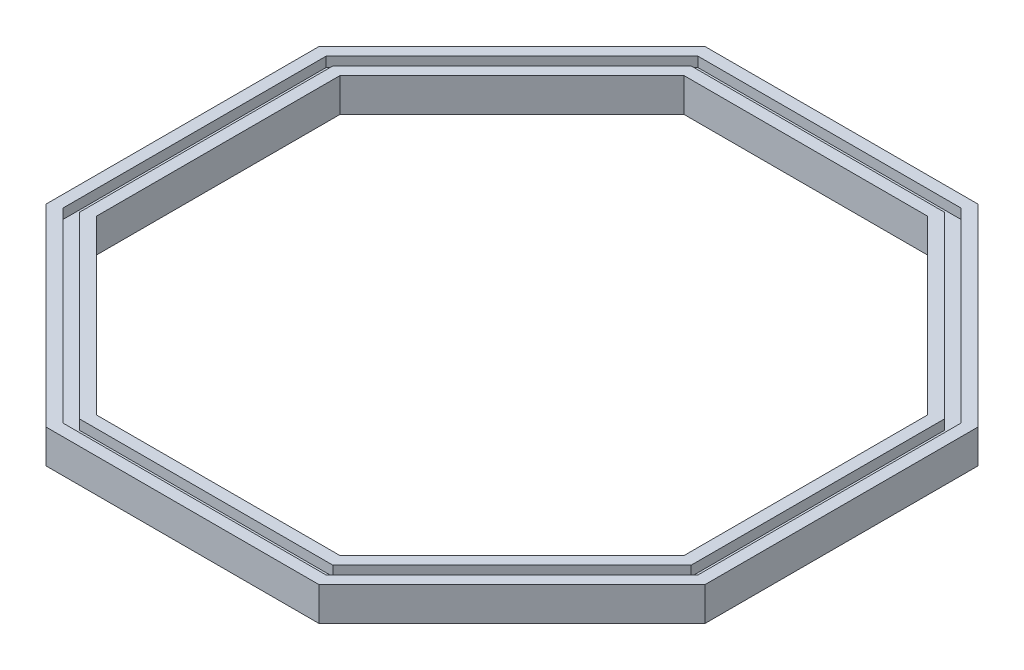
SolidWorks part; units mm, degrees
ref_plane "정면" through (0, 0, 0) normal (0, 0, 1) x (1, 0, 0)
ref_plane "윗면" through (0, 0, 0) normal (0, 1, 0) x (1, 0, 0)
ref_plane "우측면" through (0, 0, 0) normal (1, 0, 0) x (0, 0, -1)
sketch "스케치1" plane through (0, 0, 0) normal (0, 1, 0) x (1, 0, 0)
  line L0 (-55, 0) -> (55, 0) construction
  line L1 (13.2795, -32.0597) -> (32.0597, -13.2795)
  line L2 (32.0597, -13.2795) -> (32.0597, 13.2795)
  line L3 (32.0597, 13.2795) -> (13.2795, 32.0597)
  line L4 (13.2795, 32.0597) -> (-13.2795, 32.0597)
  line L5 (-13.2795, 32.0597) -> (-32.0597, 13.2795)
  line L6 (-32.0597, 13.2795) -> (-32.0597, -13.2795)
  line L7 (-32.0597, -13.2795) -> (-13.2795, -32.0597)
  line L8 (-13.2795, -32.0597) -> (13.2795, -32.0597)
  line L9 (13.7766, -33.2597) -> (33.2597, -13.7766)
  line L10 (33.2597, -13.7766) -> (33.2597, 13.7766)
  line L11 (33.2597, 13.7766) -> (13.7766, 33.2597)
  line L12 (13.7766, 33.2597) -> (-13.7766, 33.2597)
  line L13 (-13.7766, 33.2597) -> (-33.2597, 13.7766)
  line L14 (-33.2597, 13.7766) -> (-33.2597, -13.7766)
  line L15 (-33.2597, -13.7766) -> (-13.7766, -33.2597)
  line L16 (-13.7766, -33.2597) -> (13.7766, -33.2597)
  line L17 (12.7825, -30.8597) -> (30.8597, -12.7825)
  line L18 (30.8597, -12.7825) -> (30.8597, 12.7825)
  line L19 (30.8597, 12.7825) -> (12.7825, 30.8597)
  line L20 (12.7825, 30.8597) -> (-12.7825, 30.8597)
  line L21 (-12.7825, 30.8597) -> (-30.8597, 12.7825)
  line L22 (-30.8597, 12.7825) -> (-30.8597, -12.7825)
  line L23 (-30.8597, -12.7825) -> (-12.7825, -30.8597)
  line L24 (-12.7825, -30.8597) -> (12.7825, -30.8597)
  circle A0 centre (0, 0) radius 34.7011 construction
  dimension "D1" = 72
  dimension "D2" = 1.2
  dimension "D3" = 1.2
extrude "보스-돌출1" add sketch "스케치1" along normal blind 1.7 contours L15 L16 L9 L10 L11 L12 L13 L14 L8 L7 L6 L5 L4 L3 L2 L1 | L7 L8 L1 L2 L3 L4 L5 L6 L24 L23 L22 L21 L20 L19 L18 L17 | L23 L24 L17 L18 L19 L20 L21 L22
sketch "스케치2" plane through (0, 1.7, 0) normal (0, 1, 0) x (1, 0, 0)
  line L8 (-30.8597, -12.7825) -> (-12.7825, -30.8597)
  line L9 (-12.7825, -30.8597) -> (12.7825, -30.8597)
  line L10 (12.7825, -30.8597) -> (30.8597, -12.7825)
  line L11 (30.8597, -12.7825) -> (30.8597, 12.7825)
  line L12 (30.8597, 12.7825) -> (12.7825, 30.8597)
  line L13 (12.7825, 30.8597) -> (-12.7825, 30.8597)
  line L14 (-12.7825, 30.8597) -> (-30.8597, 12.7825)
  line L15 (-30.8597, 12.7825) -> (-30.8597, -12.7825)
  line L16 (-32.0597, -13.2795) -> (-13.2795, -32.0597)
  line L17 (-13.2795, -32.0597) -> (13.2795, -32.0597)
  line L18 (13.2795, -32.0597) -> (32.0597, -13.2795)
  line L19 (32.0597, -13.2795) -> (32.0597, 13.2795)
  line L20 (32.0597, 13.2795) -> (13.2795, 32.0597)
  line L21 (13.2795, 32.0597) -> (-13.2795, 32.0597)
  line L22 (-13.2795, 32.0597) -> (-32.0597, 13.2795)
  line L23 (-32.0597, 13.2795) -> (-32.0597, -13.2795)
  line L24 (-32.0597, -13.2795) -> (-13.2795, -32.0597)
  line L25 (-13.2795, -32.0597) -> (13.2795, -32.0597)
  line L26 (13.2795, -32.0597) -> (32.0597, -13.2795)
  line L27 (32.0597, -13.2795) -> (32.0597, 13.2795)
  line L28 (32.0597, 13.2795) -> (13.2795, 32.0597)
  line L29 (13.2795, 32.0597) -> (-13.2795, 32.0597)
  line L30 (-13.2795, 32.0597) -> (-32.0597, 13.2795)
  line L31 (-32.0597, 13.2795) -> (-32.0597, -13.2795)
  dimension "D1" = 1.2
  dimension "D2" = 1.2
extrude "컷-돌출3" cut sketch "스케치2" against normal blind 1
sketch "스케치3" plane through (0, 1.7, 0) normal (0, 1, 0) x (1, 0, 0)
  line L16 (-12.2854, 29.6597) -> (-29.6597, 12.2854)
  line L17 (-29.6597, 12.2854) -> (-29.6597, -12.2854)
  line L18 (-29.6597, -12.2854) -> (-12.2854, -29.6597)
  line L19 (-12.2854, -29.6597) -> (12.2854, -29.6597)
  line L20 (12.2854, -29.6597) -> (29.6597, -12.2854)
  line L21 (29.6597, -12.2854) -> (29.6597, 12.2854)
  line L22 (29.6597, 12.2854) -> (12.2854, 29.6597)
  line L23 (12.2854, 29.6597) -> (-12.2854, 29.6597)
  line L24 (-12.2854, 29.6597) -> (-29.6597, 12.2854)
  line L25 (-29.6597, 12.2854) -> (-29.6597, -12.2854)
  line L26 (-29.6597, -12.2854) -> (-12.2854, -29.6597)
  line L27 (-12.2854, -29.6597) -> (12.2854, -29.6597)
  line L28 (12.2854, -29.6597) -> (29.6597, -12.2854)
  line L29 (29.6597, -12.2854) -> (29.6597, 12.2854)
  line L30 (29.6597, 12.2854) -> (12.2854, 29.6597)
  line L31 (12.2854, 29.6597) -> (-12.2854, 29.6597)
  dimension "D1" = 1.2
extrude "컷-돌출4" cut sketch "스케치3" against normal through all
mirror "대칭 복사1" about plane through (0, 0, 0) normal (0, 1, 0) of "컷-돌출4", "컷-돌출3", "보스-돌출1"
